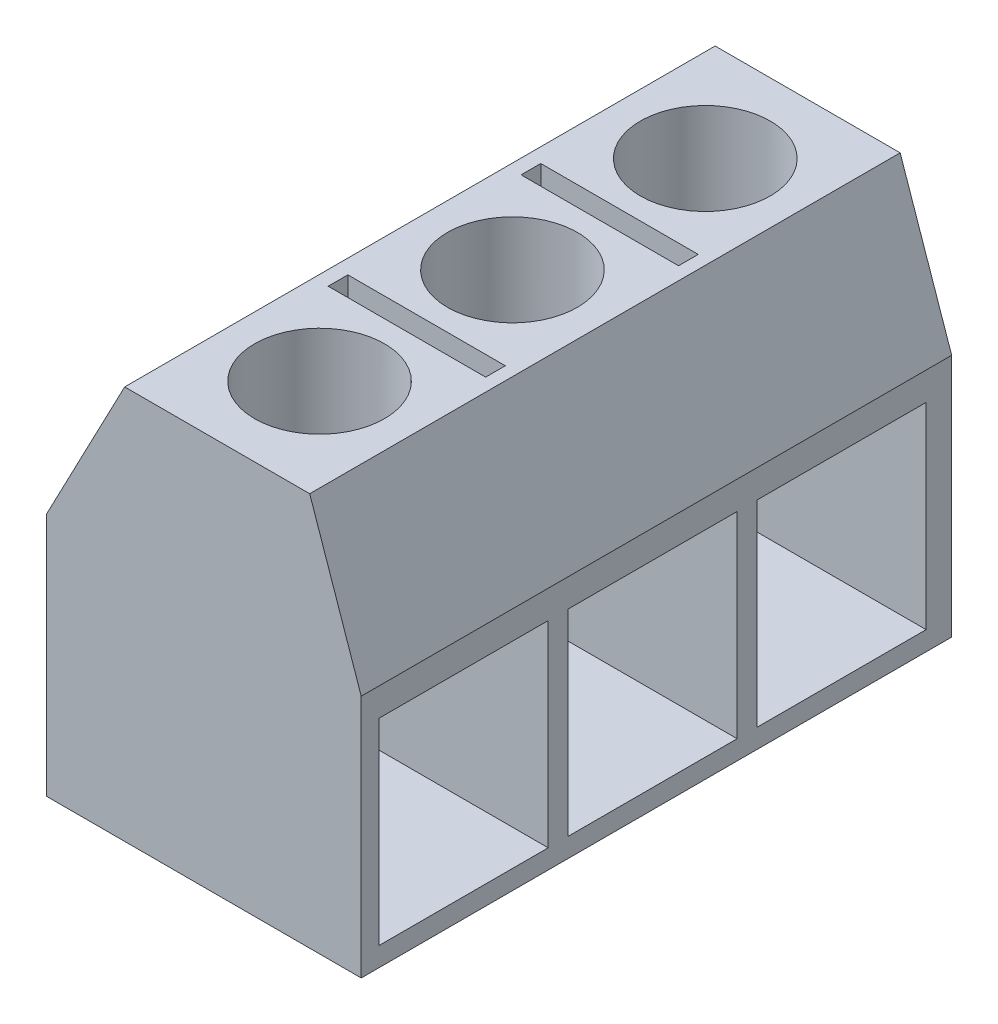
SolidWorks part; units mm, degrees
ref_plane "Front Plane" through (0, 0, 0) normal (0, 0, 1) x (1, 0, 0)
ref_plane "Top Plane" through (0, 0, 0) normal (0, 1, 0) x (1, 0, 0)
ref_plane "Right Plane" through (0, 0, 0) normal (1, 0, 0) x (0, 0, -1)
sketch "Sketch1" plane through (0, 0, 0) normal (0, 0, 1) x (1, 0, 0)
  line L6 (-363.8357, 0) -> (-355.8357, 0)
  line L7 (-355.8357, 0) -> (-355.8357, 6.2)
  line L8 (-355.8357, 6.2) -> (-357.1447, 10)
  line L9 (-357.1447, 10) -> (-361.8447, 10)
  line L10 (-361.8447, 10) -> (-363.8357, 6.2)
  line L11 (-363.8357, 6.2) -> (-363.8357, 0)
  dimension "D1" = 3.8
  dimension "D2" = 8
  dimension "D3" = 6.2
  dimension "D5" = 4.29
  dimension "D6" = 4.7
  dimension "D7" = 4.7
extrude "Boss-Extrude1" add sketch "Sketch1" along normal blind 15
ref_plane "Plane1" through (0, 10, 0) normal (0, 1, 0) x (1, 0, 0)
sketch "Sketch2" plane through (0, 10, 0) normal (0, 1, 0) x (1, 0, 0)
  line L0 (-359.4947, 0) -> (-359.4947, -2.6)
  line L1 (-357.1447, 0) -> (-361.8447, 0) construction
  line L2 (-361.8447, -15) -> (-361.8447, 0) construction
  line L3 (-357.475, -4.8) -> (-361.475, -4.8)
  line L4 (-357.475, -4.8) -> (-357.475, -5.3)
  line L5 (-357.475, -5.3) -> (-361.475, -5.3)
  line L6 (-361.475, -4.8) -> (-361.475, -5.3)
  line L11 (-357.475, -10.2) -> (-357.475, -9.7)
  line L12 (-357.475, -10.2) -> (-361.475, -10.2)
  line L13 (-361.475, -10.2) -> (-361.475, -9.7)
  line L14 (-357.475, -9.7) -> (-361.475, -9.7)
  circle A0 centre (-359.4947, -2.6) radius 1.65
  circle A1 centre (-359.4947, -7.5) radius 1.65
  circle A2 centre (-359.4947, -12.4) radius 1.65
  point P5 (-359.475, -5.05)
  point P12 (-359.475, -4.8)
  dimension "D1" = 3.3
  dimension "D2" = 2.6
  dimension "D3" = 2.35
  dimension "D4" = 2.2
  dimension "D5" = 4
  dimension "D6" = 0.5
extrude "Cut-Extrude1" cut sketch "Sketch2" against normal blind 9.2
sketch "Sketch3" plane through (-355.8357, 0, 0) normal (1, 0, 0) x (0, 0, -1)
  line L0 (-15, 3.1) -> (-14.55, 3.1)
  line L1 (-15, 0) -> (-15, 6.2) construction
  line L2 (-9.75, 5.489) -> (-5.45, 5.489)
  line L3 (-14.55, 5.489) -> (-10.25, 5.489)
  line L4 (-14.55, 5.489) -> (-14.55, 0.489)
  line L5 (-14.55, 0.489) -> (-10.25, 0.489)
  line L6 (-10.25, 5.489) -> (-10.25, 0.489)
  line L7 (-9.75, 5.489) -> (-9.75, 0.489)
  line L8 (-9.75, 0.489) -> (-5.45, 0.489)
  line L9 (-5.45, 5.489) -> (-5.45, 0.489)
  line L10 (-4.95, 5.489) -> (-0.65, 5.489)
  line L11 (-4.95, 5.489) -> (-4.95, 0.489)
  line L12 (-4.95, 0.489) -> (-0.65, 0.489)
  line L13 (-0.65, 5.489) -> (-0.65, 0.489)
  dimension "D1" = 0.45
  dimension "D2" = 5
  dimension "D3" = 4.3
  dimension "D4" = 3
extrude "Cut-Extrude2" cut sketch "Sketch3" against normal blind 5.8 contours L6 L3 L4 L5 | L9 L2 L7 L8 | L13 L10 L11 L12
